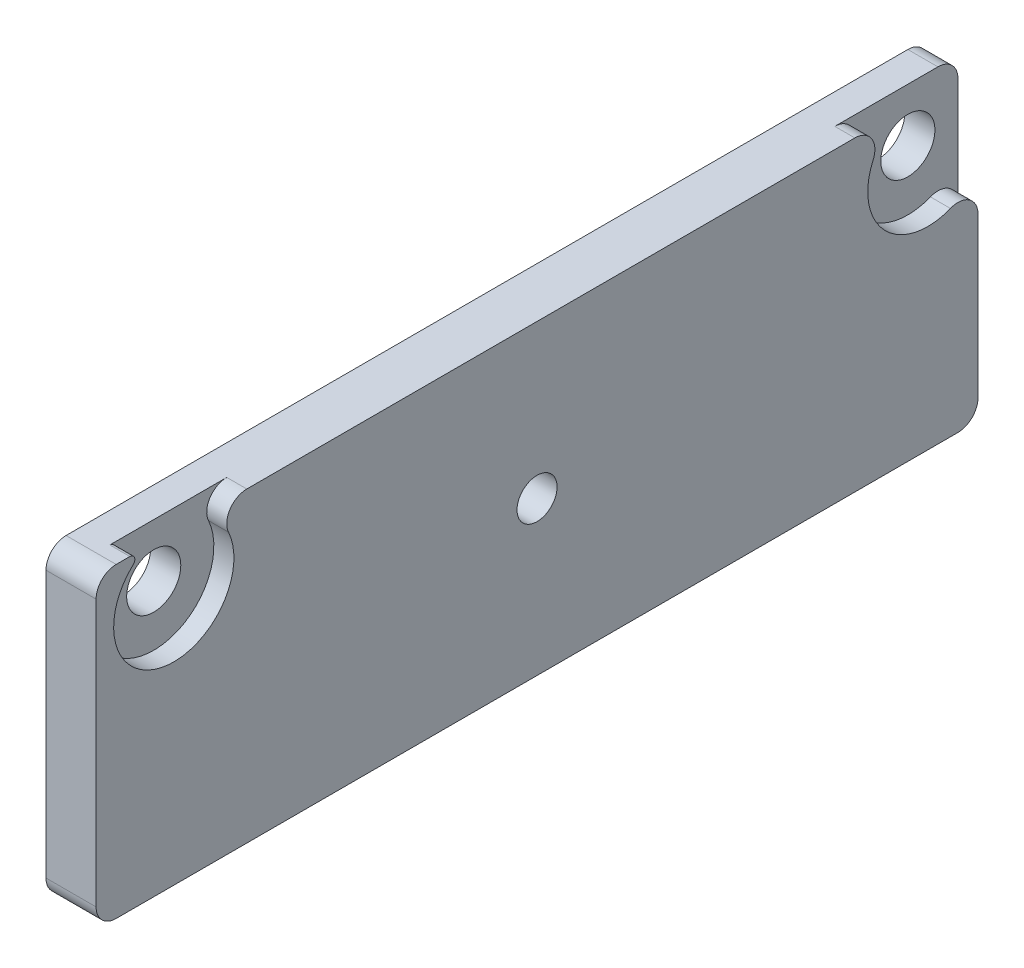
SolidWorks part; units mm, degrees
material "ABS"
ref_plane "Front Plane" through (0, 0, 0) normal (0, 0, 1) x (1, 0, 0)
ref_plane "Top Plane" through (0, 0, 0) normal (0, 1, 0) x (1, 0, 0)
ref_plane "Right Plane" through (0, 0, 0) normal (1, 0, 0) x (0, 0, -1)
sketch "Sketch1" plane through (0, 0, 0) normal (1, 0, 0) x (0, 0, -1)
  line L0 (-18.125, 5) -> (19.5, 5) construction
  line L1 (-22, -7.65) -> (22, -7.65)
  line L2 (-22, -7.65) -> (-22, 7.65)
  line L3 (-22, 7.65) -> (22, 7.65)
  line L4 (22, -7.65) -> (22, 7.65)
  line L5 (-22, -7.65) -> (22, 7.65) construction
  line L6 (-22, 7.65) -> (22, -7.65) construction
  circle A0 centre (0, 0) radius 1
  point P0 (0, 0)
  dimension "D6" = 2
  dimension "D1" = 15.3
  dimension "D2" = 44
  dimension "D3" = 2.65
  dimension "D4" = 3.875
  dimension "D5" = 2.5
extrude "Boss-Extrude1" add sketch "Sketch1" along normal blind 2.5
hole_wizard "CBORE for M2.5 Pan Head Machine Screw1" positions "Sketch3" profile "Sketch4" counterbore size "M2.5" standard "ANSI Metric" end condition through all
sketch "Sketch3" plane through (2.5, 0, 0) normal (1, 0, 0) x (0, 0, -1)
  point P0 (-18.125, 5)
  point P3 (19.5, 5)
sketch "Sketch4" plane through (2.5, 5, 18.125) normal (0, 1, 0) x (0, 0, -1)
  line L0 (0, 0) -> (0, 2.5)
  line L1 (0, 2.5) -> (1.35, 2.5)
  line L3 (1.35, 2.5) -> (1.35, 1)
  line L4 (1.35, 1) -> (3, 1)
  line L5 (3, 1) -> (3, 0)
  line L7 (3, 0) -> (0, 0)
  line L11 (0, -6.35) -> (0, 107.95) construction
  dimension "Thru Hole Dia." = 2.7
  dimension "Thru Hole Depth" = 2.5
  dimension "C'Bore Dia." = 6
  dimension "C'Bore Depth" = 1
sketch "Sketch5" plane through (2.5, 0, 0) normal (1, 0, 0) x (0, 0, -1)
  line L2 (-22, 7.65) -> (-22, -7.65)
  line L3 (-22, 7.65) -> (-22, -7.65)
  line L6 (22, 6.6583) -> (22, 7.65)
  line L7 (22, 6.6583) -> (22, 7.65)
  line L10 (22, 7.65) -> (20.9062, 7.65)
  line L11 (22, 7.65) -> (20.9062, 7.65)
  line L12 (-19.5312, 7.65) -> (-22, 7.65)
  line L13 (-19.5312, 7.65) -> (-22, 7.65)
  line L17 (18.0938, 7.65) -> (-16.7188, 7.65)
  line L18 (18.0938, 7.65) -> (-16.7188, 7.65)
  line L19 (-22, -7.65) -> (22, -7.65)
  line L20 (-22, -7.65) -> (22, -7.65)
  line L21 (22, -7.65) -> (22, 3.3417)
  line L22 (22, -7.65) -> (22, 3.3417)
  arc A1 (-19.5312, 7.65) -> (-16.7188, 7.65) centre (-18.125, 5) ccw
  arc A3 (22, 6.6583) -> (20.9062, 7.65) centre (19.5, 5) ccw
  arc A5 (22, 6.6583) -> (20.9062, 7.65) centre (19.5, 5) ccw
  arc A6 (-19.5312, 7.65) -> (-16.7188, 7.65) centre (-18.125, 5) ccw
  arc A8 (18.0938, 7.65) -> (22, 3.3417) centre (19.5, 5) ccw
  arc A9 (18.0938, 7.65) -> (22, 3.3417) centre (19.5, 5) ccw
  dimension "D1" = 0
  dimension "D2" = 0
extrude "Cut-Extrude1" cut sketch "Sketch5" against normal up to surface (1 mm away) contours A5 L7 L11 up to face at (1.5, 5, 16.775)
fillet "Fillet1" radius 1 7 edges at (2, 7.65, -18.0938) (2, 7.65, 16.7188) (1.25, 7.65, 22) (0.75, 7.65, -22) (1.25, -7.65, -22) (1.25, -7.65, 22) (2, 3.3417, -22)
fillet "Fillet2" radius 0.25 1 edges at (2, 7.65, 19.5312)
